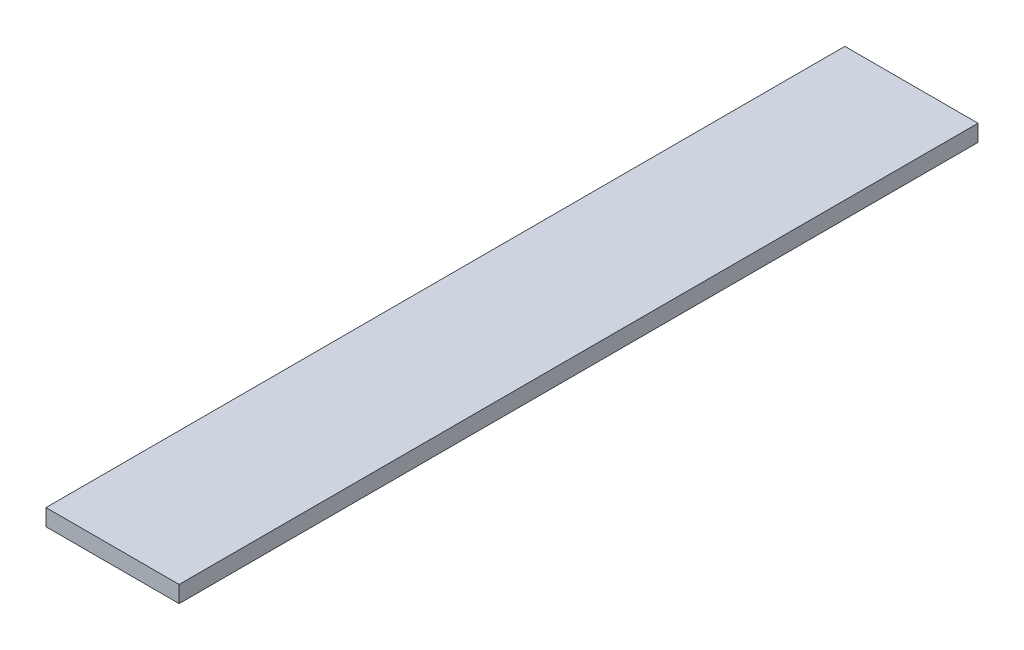
SolidWorks part; units mm, degrees
ref_plane "Front Plane" through (0, 0, 0) normal (0, 0, 1) x (1, 0, 0)
ref_plane "Top Plane" through (0, 0, 0) normal (0, 1, 0) x (1, 0, 0)
ref_plane "Right Plane" through (0, 0, 0) normal (1, 0, 0) x (0, 0, -1)
sketch "Sketch1" plane through (0, 0, 0) normal (0, 1, 0) x (1, 0, 0)
  line L1 (0, 0) -> (50.8, 0)
  line L2 (0, 0) -> (0, 304.8)
  line L3 (0, 304.8) -> (50.8, 304.8)
  line L4 (50.8, 0) -> (50.8, 304.8)
  dimension "D1" = 304.8
  dimension "D2" = 50.8
extrude "Boss-Extrude1" add sketch "Sketch1" along normal blind 6.35
